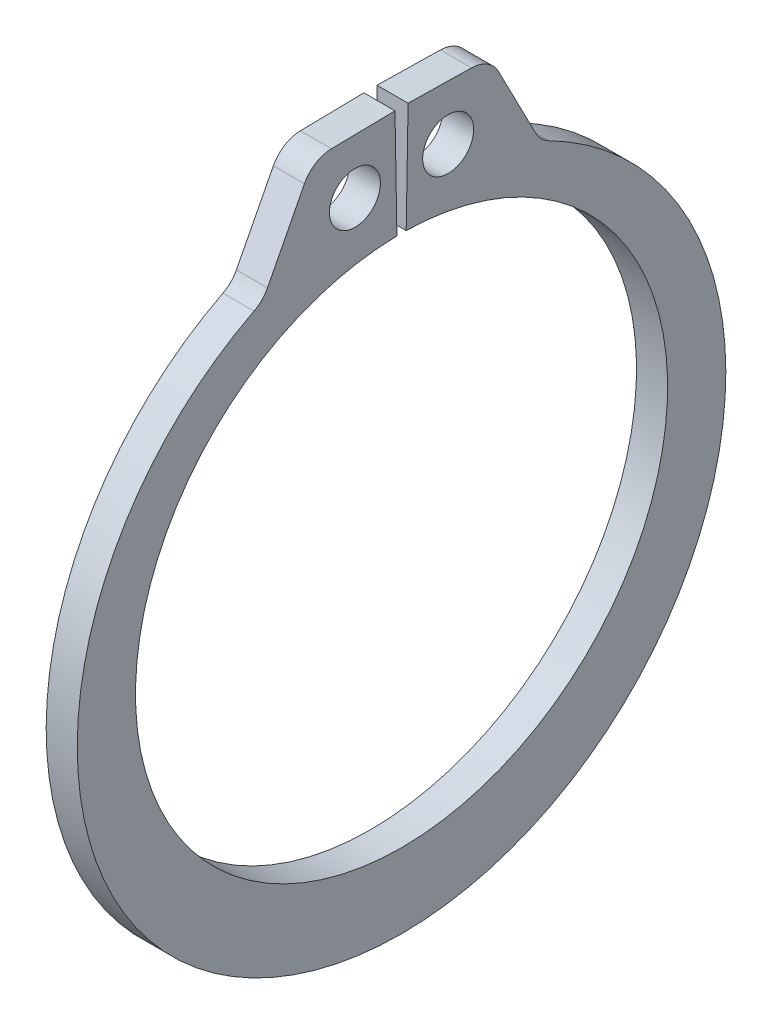
SolidWorks part; units mm, degrees
material "Cast Carbon Steel"
ref_plane "Front" through (0, 0, 0) normal (0, 0, 1) x (1, 0, 0)
ref_plane "Top" through (0, 0, 0) normal (0, 1, 0) x (1, 0, 0)
ref_plane "Right" through (0, 0, 0) normal (1, 0, 0) x (0, 0, -1)
sketch "Sketch1" plane through (0, 0, 0) normal (1, 0, 0) x (0, 0, -1)
  line L0 (0, 0) -> (0, 5.4356) construction
  line L1 (-0.0949, 5.4348) -> (-0.1339, 7.6696)
  line L2 (0.1339, 7.6696) -> (1.81, 7.6404)
  line L3 (1.81, 7.6404) -> (2.8346, 5.6538)
  line L4 (0.0949, 5.4348) -> (0.1339, 7.6696)
  line L5 (-0.1339, 7.6696) -> (-1.81, 7.6404)
  line L6 (-1.81, 7.6404) -> (-2.8346, 5.6538)
  line L7 (-2.8346, 5.6538) -> (-2.4361, 4.8591) construction
  line L8 (2.8346, 5.6538) -> (2.4361, 4.8591) construction
  line L9 (0, -5.4356) -> (0, -6.9596) construction
  line L10 (-1.81, 7.6404) -> (-0.0949, 5.4348) construction
  line L11 (0, 5.4356) -> (0, 7.6708) construction
  line L12 (-5.4356, 0) -> (5.4356, 0) construction
  circle A0 centre (0, 0) radius 5.4356 construction
  arc A1 (-0.0949, 5.4348) -> (0.0949, 5.4348) centre (0, 0) ccw
  circle A3 centre (0, 0) radius 8.636 construction
  circle A4 centre (-0.9524, 6.5376) radius 0.5207
  circle A5 centre (0.9524, 6.5376) radius 0.5207
  arc A6 (-2.8346, 5.6538) -> (2.8346, 5.6538) centre (0, -0.3344) ccw
  point P0 (0, -6.9596)
  dimension "A" = 10.8712
  dimension "Hole" = 1.0414
  dimension "Smin" = 0.889
  dimension "H" = 2.2352
  dimension "D2" = 1.6764
  dimension "Angle" = 1
extrude "Extrude1" add sketch "Sketch1" along normal mid plane 0.635
fillet "Fillet1" radius 0.635 4 edges at (0, 5.6538, 2.8346) (0, 5.6538, -2.8346) (0, 7.6404, 1.81) (0, 7.6404, -1.81)
sketch "Sketch2" plane through (0, 0, 0) normal (0, 0, 1) x (1, 0, 0)
  line L0 (-3.5433, 0) -> (9.1567, 0)
  line L1 (9.1567, 0) -> (9.1567, -5.9563)
  line L2 (-3.5433, 0) -> (-3.5433, -5.6261)
  line L3 (9.1567, -5.9563) -> (0.3683, -5.9563)
  line L4 (0.3683, -5.9563) -> (0.3683, -5.6261)
  line L5 (0.3683, -5.6261) -> (-0.3683, -5.6261)
  line L6 (-0.3683, -5.6261) -> (-0.3683, -5.9563)
  line L7 (-0.3683, -5.9563) -> (-3.5433, -5.9563) construction
  line L8 (-3.5433, -5.9563) -> (-3.5433, 0) construction
  line L9 (9.1567, 0) -> (76.391, 0) construction
  line L10 (0, -5.6261) -> (0, 0) construction
  line L11 (-3.5433, -5.6261) -> (-3.2131, -5.9563)
  line L12 (-3.2131, -5.9563) -> (-0.3683, -5.9563)
  dimension "D2" = 12.7
  dimension "D3" = 3.175
  dimension "D1" = 45
revolve "Revolve1" [suppressed] add sketch "Sketch2" angle 360 about L9
delete or keep bodies "Body-Delete1" [suppressed] type delete bodies bodies 122
equation "\"D2@Sketch2\" = \"D1@Extrude1\"*20"
equation "\"D3@Sketch2\" = \"D2@Sketch2\"/4"
equation "\"D2@Sketch1\" = \"H@Sketch1\"*.75"
equation "\"D1@Fillet1\" = \"D1@Extrude1\""
